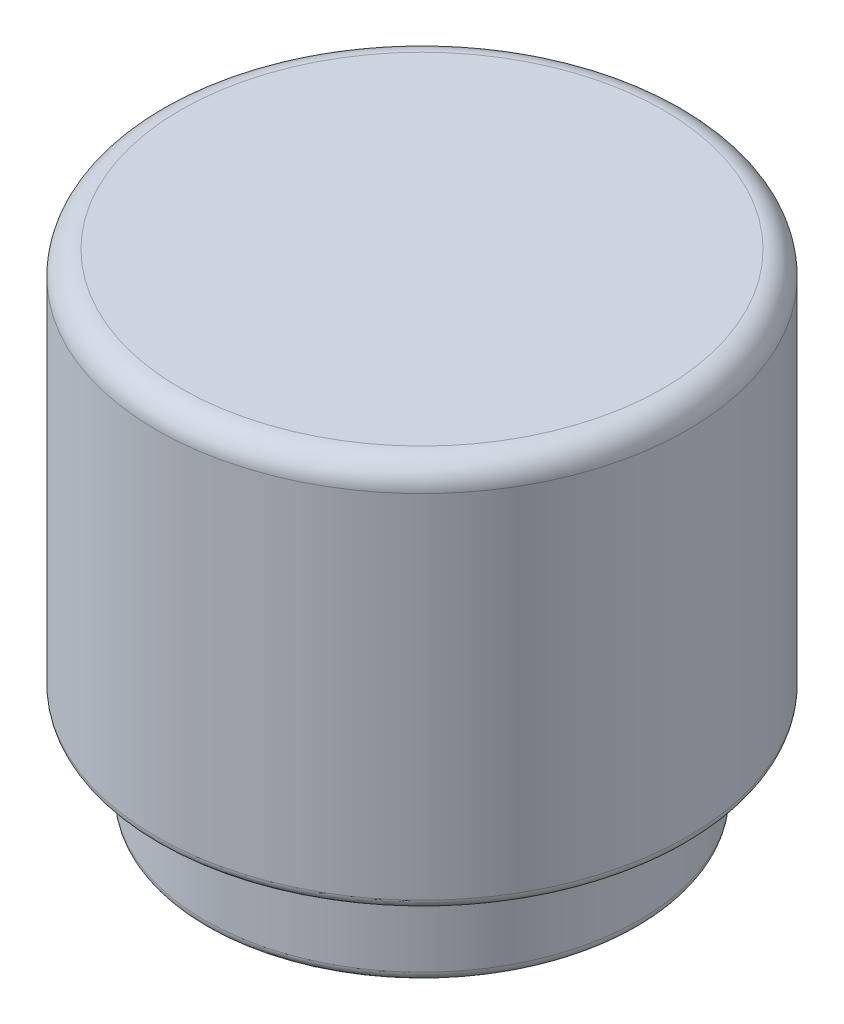
SolidWorks part; units mm, degrees
ref_plane "Front Plane" through (0, 0, 0) normal (0, 0, 1) x (1, 0, 0)
ref_plane "Top Plane" through (0, 0, 0) normal (0, 1, 0) x (1, 0, 0)
ref_plane "Right Plane" through (0, 0, 0) normal (1, 0, 0) x (0, 0, -1)
sketch "Sketch1" plane through (0, 0, 0) normal (1, 0, 0) x (0, 0, -1)
  line L0 (0, 0) -> (0, -10) construction
  line L1 (0, 0) -> (-5.5, 0)
  line L2 (0, -0.5) -> (-5, -0.5)
  line L3 (-4.5, -8) -> (-5.5, -8)
  line L4 (-5.5, 0) -> (-5.5, -8)
  line L5 (-5, -0.5) -> (-5, -7.5)
  line L6 (-4.5, -8) -> (-4.5, -10)
  line L7 (-4.5, -10) -> (0, -10) construction
  line L8 (-4, -7.5) -> (-5, -7.5)
  line L9 (-4, -7.5) -> (-4, -10)
  line L10 (0, 0) -> (0, -0.5)
  line L11 (-4, -10) -> (-4.5, -10)
  dimension "D1" = 8
  dimension "D2" = 5.5
  dimension "D3" = 10
  dimension "D4" = 4.5
  dimension "D5" = 0.5
revolve "Revolve1" add sketch "Sketch1" angle 360 about L0
fillet "Fillet1" radius 0.5 1 edges at (0, 0, 5.5)
fillet "Fillet2" radius 0.2 5 edges at (0, -0.5, 5) (0, -7.5, 4) (0, -10, 4) (0, -10, 4.5) (0, -8, 5.5)
